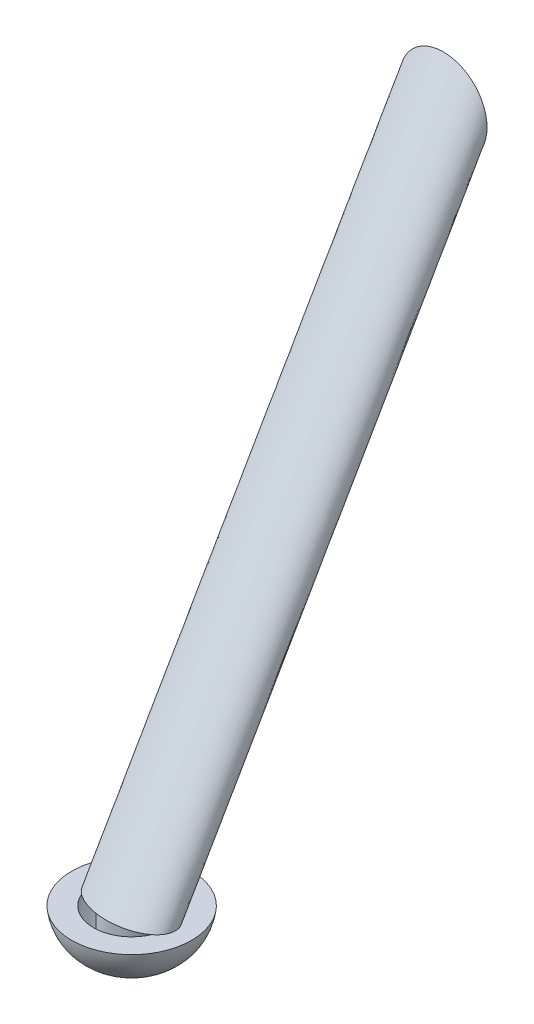
SolidWorks part; units mm, degrees
material "7075-T6 (SN)"
ref_plane "Front Plane" through (0, 0, 0) normal (0, 0, 1) x (1, 0, 0)
ref_plane "Top Plane" through (0, 0, 0) normal (0, 1, 0) x (1, 0, 0)
ref_plane "Right Plane" through (0, 0, 0) normal (1, 0, 0) x (0, 0, -1)
sketch "Sketch1" plane through (0, 0, 0) normal (1, 0, 0) x (0, 0, -1)
  line L0 (0, 0) -> (-1175.8461, -2036.6253)
  line L1 (0, 0) -> (0, -884.2253)
  line L2 (0, -884.2253) -> (-765.7615, -1326.3379)
  dimension "D1" = 30
  dimension "D2" = 1152.4
  dimension "D3" = 120
sketch "Sketch2" plane through (0, 0, 0) normal (0, 0, 1) x (1, 0, 0)
  circle A0 centre (0, 0) radius 152.4
  circle A1 centre (0, 0) radius 139.7
  dimension "D1" = 304.8
  dimension "D2" = 279.4
sweep "Sweep2" add profiles "Sketch2" path "Sketch1"
sketch "Sketch5" plane through (0, 0, 1175.8461) normal (0, 0, 1) x (1, 0, 0)
  line L0 (0, 0) -> (0, -2036.6253) construction
  circle A0 centre (0, -2036.6253) radius 152.4 construction
  point P0 (0, -1884.2253)
ref_plane "Plane2" through (0, -1884.2253, 0) normal (0, 1, 0) x (1, 0, 0)
sketch "Sketch6" plane through (0, -1884.2253, 0) normal (0, 1, 0) x (1, 0, 0)
  circle A0 centre (0, -1175.8461) radius 415.386
extrude "Cut-Extrude2" cut sketch "Sketch6" against normal through all contours A0
sketch "Sketch7" plane through (0, 0, 0) normal (1, 0, 0) x (0, 0, -1)
  line L0 (0, 0) -> (-1175.8461, -2036.6253) construction
  line L1 (-1220.8876, -1884.2253) -> (-1297.0876, -1884.2253)
  line L2 (0, 0) -> (-1175.8461, -2036.6253) construction
  line L5 (-1087.858, -1884.2253) -> (-1087.858, -2036.6253)
  line L6 (-1175.8461, -1884.2253) -> (-1175.8461, -1975.6662)
  line L7 (-1175.8461, -1884.2253) -> (-1087.858, -1884.2253)
  arc A1 (-1175.8461, -1975.6662) -> (-1220.8876, -1884.2253) centre (-1119.521, -1891.1083) cw
  arc A2 (-1297.0876, -1884.2253) -> (-1087.858, -2036.6253) centre (-1120.6968, -1861.8842) ccw
  point P4 (-1087.858, -1884.2253)
  dimension "D1" = 152.4
  dimension "D2" = 101.6
  dimension "D4" = 177.8
  dimension "D3" = 76.2
revolve "Revolve1" add sketch "Sketch7" angle 360 about L5
sketch3d "3DSketch1"
  line L0 (-625, -785.072, -171.7385) -> (0, -1326.3379, 765.7615)
  line L2 (0, -884.2253, 0) -> (0, -1326.3379, 765.7615) construction
  point P0 (0, -1326.3379, 765.7615)
  point P2 (0, -884.2253, 0)
  point P5 (-625, -785.072, -171.7385)
  dimension "D2" = 625
  dimension "D1" = 30
ref_plane "Plane4" through (0, 0, -171.7385) normal (0, 0, 1) x (1, 0, 0)
sketch "Sketch22" plane through (0, 0, -171.7385) normal (0, 0, 1) x (1, 0, 0)
  circle A0 centre (-625, -785.072) radius 76.2
  dimension "D1" = 152.4
sweep "Sweep6" [suppressed] add profiles "Sketch22" path "3DSketch1"
mirror "Mirror2" [suppressed] about plane through (0, 0, 0) normal (1, 0, 0)
